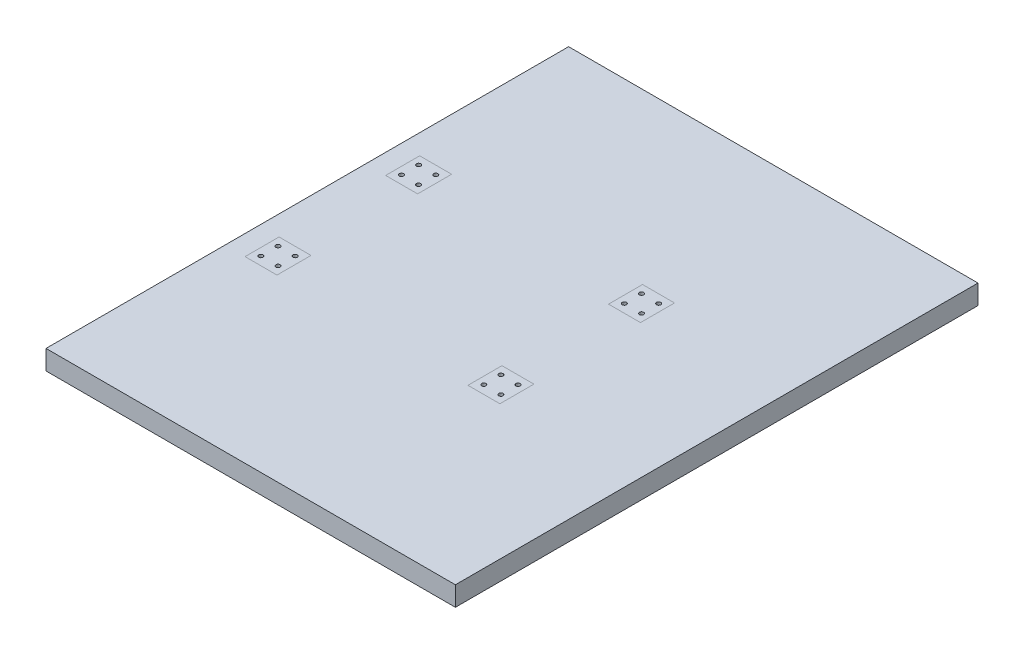
SolidWorks part; units mm, degrees
material "Alloy Steel"
ref_plane "Front Plane" through (0, 0, 0) normal (0, 0, 1) x (1, 0, 0)
ref_plane "Top Plane" through (0, 0, 0) normal (0, 1, 0) x (1, 0, 0)
ref_plane "Right Plane" through (0, 0, 0) normal (1, 0, 0) x (0, 0, -1)
sketch "Sketch1" plane through (0, 0, 0) normal (0, 1, 0) x (1, 0, 0)
  line L0 (-366.1707, 0) -> (17942.3634, 0) construction
  line L1 (0, -366.1707) -> (0, 17942.3634) construction
  line L2 (-584.2, 254) -> (-482.6, 254)
  line L3 (-584.2, -355.6) -> (584.2, -355.6)
  line L4 (-584.2, -355.6) -> (-584.2, 355.6)
  line L5 (-584.2, 355.6) -> (584.2, 355.6)
  line L6 (584.2, -355.6) -> (584.2, 355.6)
  line L7 (0, 355.6) -> (0, -355.6) construction
  line L8 (-584.2, 0) -> (584.2, 0) construction
  line L9 (-482.6, 254) -> (-482.6, 355.6)
  line L10 (482.6, 254) -> (482.6, 355.6)
  line L11 (584.2, 254) -> (482.6, 254)
  line L12 (584.2, -254) -> (482.6, -254)
  line L13 (482.6, -254) -> (482.6, -355.6)
  line L14 (-482.6, -254) -> (-482.6, -355.6)
  line L15 (-584.2, -254) -> (-482.6, -254)
  line L16 (-533.4, 254) -> (-533.4, -254) construction
  line L17 (-552.45, 254) -> (-552.45, -254)
  line L18 (-514.35, 254) -> (-514.35, -254)
  line L19 (514.35, 254) -> (514.35, -254)
  line L20 (552.45, 254) -> (552.45, -254)
  line L21 (-514.35, 25.4) -> (514.35, 25.4)
  line L22 (-514.35, -25.4) -> (514.35, -25.4)
  point P4 (0, 0)
  dimension "D1" = 1168.4
  dimension "D2" = 711.2
  dimension "D3" = 101.6
  dimension "D4" = 38.1
  dimension "D5" = 50.8
extrude "Boss-Extrude1" add sketch "Sketch1" against normal blind 704.85 contours L2 L9 L5 L4 | L11 L6 L5 L10 | L12 L13 L3 L6 | L15 L4 L3 L14 | L18 L2 L17 L15 | L18 L22 L19 L21 | L20 L11 L19 L12
sketch "Sketch2" plane through (0, 0, 0) normal (1, 0, 0) x (0, 0, -1)
  line L0 (254, -704.85) -> (254, 0) construction
  line L1 (-254, 0) -> (254, 0)
  line L2 (-254, 0) -> (-254, -100)
  line L3 (-254, -100) -> (254, -100)
  line L4 (254, 0) -> (254, -100)
  line L5 (-254, -704.85) -> (-254, 0) construction
  line L6 (-254, -150.8) -> (254, -150.8)
  line L7 (-254, -150.8) -> (-254, -554.05)
  line L8 (-254, -554.05) -> (254, -554.05)
  line L9 (254, -150.8) -> (254, -554.05)
  line L10 (254, -704.85) -> (254, 0) construction
  line L11 (-254, -704.85) -> (254, -704.85)
  line L12 (-254, -704.85) -> (-254, -604.85)
  line L13 (-254, -604.85) -> (254, -604.85)
  line L14 (254, -704.85) -> (254, -604.85)
  dimension "D1" = 100
  dimension "D2" = 50.8
  dimension "D3" = 50.8
extrude "Cut-Extrude1" cut sketch "Sketch2" against normal through all both and the other way through all
sketch "Sketch3" plane through (0, 0, 0) normal (0, 1, 0) x (1, 0, 0)
  line L0 (-584.2, -355.6) -> (-482.6, -355.6) construction
  line L1 (-596.9, 393.7) -> (596.9, 393.7)
  line L2 (-596.9, 393.7) -> (-596.9, -368.3)
  line L3 (-596.9, -368.3) -> (596.9, -368.3)
  line L4 (596.9, 393.7) -> (596.9, -368.3)
  line L5 (0, -368.3) -> (0, 393.7) construction
  line L6 (-596.9, 12.7) -> (596.9, 12.7) construction
  point P0 (0, 12.7)
  dimension "D1" = 762
  dimension "D2" = 1193.8
  dimension "D3" = 12.7
extrude "Boss-Extrude2" add sketch "Sketch3" along normal blind 28.5 separate body
sketch "Sketch4" plane through (0, 28.5, 0) normal (0, 1, 0) x (1, 0, 0)
  line L0 (-596.9, 20) -> (596.9, 20) construction
  line L1 (-596.9, 393.7) -> (-596.9, -368.3) construction
  line L2 (596.9, -368.3) -> (596.9, 393.7) construction
  line L3 (-556.9, 110) -> (-531.9, 110) construction
  line L4 (-556.9, 110) -> (-556.9, 135) construction
  line L5 (-556.9, 135) -> (-231.9, 135) construction
  circle A0 centre (-556.9, 110) radius 3.1
  circle A1 centre (-531.9, 110) radius 3.1
  circle A2 centre (-531.9, 135) radius 3.1
  circle A3 centre (-556.9, 135) radius 3.1
  circle A4 centre (-231.9, 135) radius 3.1
  circle A5 centre (-206.9, 135) radius 3.1
  circle A6 centre (-231.9, 110) radius 3.1
  circle A7 centre (-206.9, 110) radius 3.1
  circle A8 centre (-206.9, -70) radius 3.1
  circle A9 centre (-231.9, -70) radius 3.1
  circle A10 centre (-231.9, -95) radius 3.1
  circle A11 centre (-206.9, -95) radius 3.1
  circle A12 centre (-531.9, -70) radius 3.1
  circle A13 centre (-531.9, -95) radius 3.1
  circle A14 centre (-556.9, -70) radius 3.1
  circle A15 centre (-556.9, -95) radius 3.1
  dimension "D2" = 180
  dimension "D3" = 40
  dimension "D4" = 6.2
  dimension "D1" = 20
  dimension "D7" = 25
  dimension "D8" = 25
  dimension "D10" = 325
  dimension "D5" = 2
  dimension "D6" = 2
  dimension "D9" = 2
extrude "Cut-Extrude2" cut sketch "Sketch4" against normal up to surface (28.5 mm away) up to face at (0, 0, -12.7)
mirror "Mirror1" about plane through (0, 0, 0) normal (1, 0, 0) of "Cut-Extrude2"
sketch "Sketch5" plane through (0, 0, 0) normal (0, 0, 1) x (1, 0, 0)
  line L1 (-596.9, 28.5) -> (0, 28.5)
  line L2 (-596.9, 28.5) -> (-596.9, 0)
  line L3 (-596.9, 0) -> (0, 0)
  line L4 (0, 28.5) -> (0, 0)
  circle A0 centre (0, 0) radius 1000
  dimension "D1" = 2000
extrude "Cut-Extrude3" cut sketch "Sketch5" against normal through all both and the other way through all contours A0 L1 L4 L3 L2
sketch "Sketch6" plane through (0, 28.5, 0) normal (0, 1, 0) x (1, 0, 0)
  line L0 (-521.1, -57.7053) -> (-521.1, -107.3) construction
  line L1 (-521.1, -107.3) -> (-567.7, -107.3) construction
  line L2 (-567.7, -107.3) -> (-567.7, -57.7053) construction
  line L3 (-567.7, -57.7053) -> (-521.1, -57.7053) construction
  line L4 (-196.1, -57.7053) -> (-196.1, -107.3) construction
  line L5 (-196.1, -107.3) -> (-242.7, -107.3) construction
  line L6 (-242.7, -107.3) -> (-242.7, -57.7053) construction
  line L7 (-242.7, -57.7053) -> (-196.1, -57.7053) construction
  line L8 (-242.7, 97.7053) -> (-242.7, 147.3) construction
  line L9 (-242.7, 147.3) -> (-196.1, 147.3) construction
  line L10 (-196.1, 147.3) -> (-196.1, 97.7053) construction
  line L11 (-196.1, 97.7053) -> (-242.7, 97.7053) construction
  line L12 (-567.7, 97.7053) -> (-567.7, 147.3) construction
  line L13 (-567.7, 147.3) -> (-521.1, 147.3) construction
  line L14 (-521.1, 147.3) -> (-521.1, 97.7053) construction
  line L15 (-521.1, 97.7053) -> (-567.7, 97.7053) construction
  line L16 (-521.1, -57.7053) -> (-521.1, -107.3)
  line L17 (-521.1, -107.3) -> (-567.7, -107.3)
  line L18 (-567.7, -107.3) -> (-567.7, -57.7053)
  line L19 (-567.7, -57.7053) -> (-521.1, -57.7053)
  line L20 (-196.1, -57.7053) -> (-196.1, -107.3)
  line L21 (-196.1, -107.3) -> (-242.7, -107.3)
  line L22 (-242.7, -107.3) -> (-242.7, -57.7053)
  line L23 (-242.7, -57.7053) -> (-196.1, -57.7053)
  line L24 (-242.7, 97.7053) -> (-242.7, 147.3)
  line L25 (-242.7, 147.3) -> (-196.1, 147.3)
  line L26 (-196.1, 147.3) -> (-196.1, 97.7053)
  line L27 (-196.1, 97.7053) -> (-242.7, 97.7053)
  line L28 (-567.7, 97.7053) -> (-567.7, 147.3)
  line L29 (-567.7, 147.3) -> (-521.1, 147.3)
  line L30 (-521.1, 147.3) -> (-521.1, 97.7053)
  line L31 (-521.1, 97.7053) -> (-567.7, 97.7053)
split line "Split Line1"
